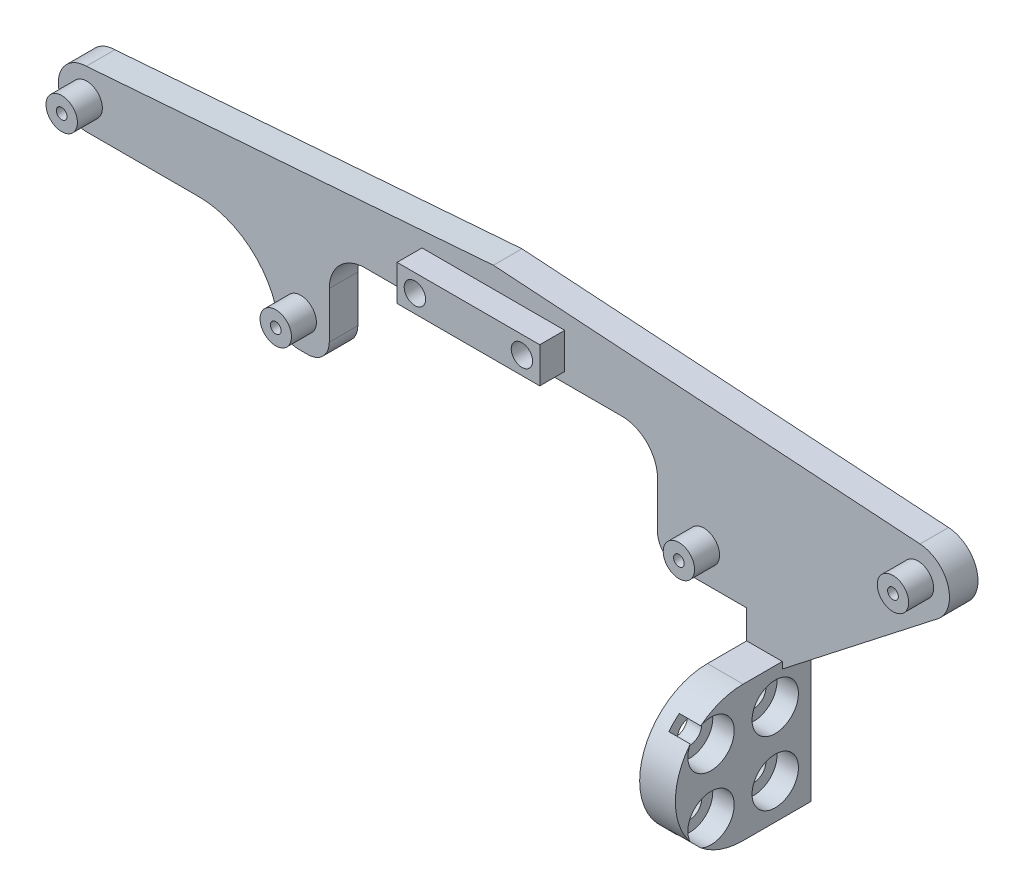
SolidWorks part; units mm, degrees
ref_plane "Front" through (0, 0, 0) normal (0, 0, 1) x (1, 0, 0)
ref_plane "Top" through (0, 0, 0) normal (0, 1, 0) x (1, 0, 0)
ref_plane "Right" through (0, 0, 0) normal (1, 0, 0) x (0, 0, -1)
sketch "Sketch1" plane through (0, 0, 0) normal (0, 0, 1) x (1, 0, 0)
  line L0 (0, 0) -> (59.7902, -3.9348)
  line L1 (62.3996, -11.6782) -> (40.5, -28.7585)
  line L2 (40.5, -28.7585) -> (40.5, -46.844)
  line L3 (40.5, -46.844) -> (35.5, -46.844)
  line L4 (35.5, -46.844) -> (35.5, -23.844)
  line L5 (35.5, -23.844) -> (23, -23.844)
  line L6 (23, -23.844) -> (23, -9.3156)
  line L7 (23, -9.3156) -> (-23, -9.3156)
  line L8 (-23, -9.3156) -> (-23, -23.844)
  line L9 (-23, -23.844) -> (-30, -23.844)
  line L10 (-30, -23.844) -> (-30, -23.6246)
  line L11 (-41.3048, -12.3198) -> (-57, -12.3198)
  line L12 (-57.0499, -4.3684) -> (0, 0)
  arc A0 (59.7902, -3.9348) -> (62.3996, -11.6782) centre (59.5, -8.344) cw
  arc A1 (-30, -23.6246) -> (-41.3048, -12.3198) centre (-41.3048, -23.6246) ccw
  arc A2 (-57, -12.3198) -> (-57.0499, -4.3684) centre (-57, -8.344) cw
  dimension "D7" = 23
  dimension "D8" = 38.5
  dimension "D1" = 46
  dimension "D2" = 5
  dimension "D3" = 19
  dimension "D4" = 12.5
  dimension "D5" = 34
  dimension "D6" = 7
  dimension "D13" = 38.5
extrude "Boss-Extrude1" add sketch "Sketch1" along normal blind 4
sketch "Sketch2" plane through (0, 0, 4) normal (0, 0, 1) x (1, 0, 0)
  circle A0 centre (59.5, -8.344) radius 2.2
  dimension "D1" = 4.4
extrude "Boss-Extrude2" add sketch "Sketch2" along normal blind 3.5
sketch "Sketch3" plane through (0, 0, 7.5) normal (0, 0, 1) x (1, 0, 0)
  circle A0 centre (59.5, -8.344) radius 0.75
  dimension "D1" = 1.5
extrude "Cut-Extrude1" cut sketch "Sketch3" against normal through all
sketch "Sketch4" plane through (0, 0, 4) normal (0, 0, 1) x (1, 0, 0)
  circle A0 centre (29.5, -19.344) radius 2.2
  circle A1 centre (59.5, -8.344) radius 0.75 construction
  dimension "D1" = 4.4
  dimension "D2" = 30
  dimension "D3" = 11
extrude "Boss-Extrude3" add sketch "Sketch4" along normal blind 3.5
sketch "Sketch5" plane through (0, 0, 7.5) normal (0, 0, 1) x (1, 0, 0)
  circle A0 centre (29.5, -19.344) radius 0.75
  dimension "D1" = 1.5
extrude "Cut-Extrude2" cut sketch "Sketch5" against normal through all
sketch "Sketch6" plane through (0, 0, 4) normal (0, 0, 1) x (1, 0, 0)
  circle A0 centre (-57, -8.344) radius 2.2
  dimension "D1" = 4.4
extrude "Boss-Extrude4" add sketch "Sketch6" along normal blind 3.5
sketch "Sketch7" plane through (0, 0, 7.5) normal (0, 0, 1) x (1, 0, 0)
  circle A0 centre (-57, -8.344) radius 0.75
  dimension "D1" = 1.5
extrude "Cut-Extrude3" cut sketch "Sketch7" against normal through all
sketch "Sketch8" plane through (0, 0, 4) normal (0, 0, 1) x (1, 0, 0)
  circle A0 centre (-27, -19.344) radius 2.2
  circle A1 centre (-57, -8.344) radius 0.75 construction
  dimension "D1" = 4.4
  dimension "D2" = 30
  dimension "D3" = 11
extrude "Boss-Extrude5" add sketch "Sketch8" along normal blind 3.5
sketch "Sketch9" plane through (0, 0, 7.5) normal (0, 0, 1) x (1, 0, 0)
  circle A0 centre (-27, -19.344) radius 0.75
  dimension "D1" = 1.5
extrude "Cut-Extrude4" cut sketch "Sketch9" against normal through all
sketch "Sketch10" plane through (0, 0, 4) normal (0, 0, 1) x (1, 0, 0)
  line L1 (-10, -2.8992) -> (10, -2.8992)
  line L2 (-10, -2.8992) -> (-10, -7.8992)
  line L3 (-10, -7.8992) -> (10, -7.8992)
  line L4 (10, -2.8992) -> (10, -7.8992)
  dimension "D1" = 5
  dimension "D2" = 20
  dimension "D3" = 10
extrude "Boss-Extrude6" add sketch "Sketch10" along normal blind 3.5
sketch "Sketch11" plane through (0, 0, 7.5) normal (0, 0, 1) x (1, 0, 0)
  line L0 (10, -2.8992) -> (-10, -2.8992) construction
  line L2 (-10, -2.8992) -> (-10, -7.8992) construction
  circle A0 centre (-7.5, -5.3992) radius 1.5
  circle A1 centre (7.5, -5.3992) radius 1.5
  dimension "D1" = 3
  dimension "D2" = 3
  dimension "D3" = 2.5
  dimension "D4" = 15
  dimension "D5" = 2.5
extrude "Cut-Extrude5" cut sketch "Sketch11" against normal through all
sketch "Sketch12" plane through (40.5, 0, 0) normal (1, 0, 0) x (0, 0, -1)
  line L0 (-4, -46.844) -> (0, -46.844) construction
  line L1 (-4, -46.844) -> (-4, -28.7585) construction
  line L2 (-9.5, -27.844) -> (-4, -27.844)
  line L3 (-4, -28.7585) -> (-4, -11.6782) construction
  line L4 (-4, -27.844) -> (-4, -29.598)
  line L5 (-9.5, -46.844) -> (-4, -46.844)
  line L6 (-4, -46.844) -> (-4, -45.0899)
  line L7 (-4, -29.598) -> (-4, -45.0899)
  line L9 (-9.5, -27.844) -> (-4, -27.844)
  line L10 (-9.5, -27.844) -> (-9.5, -46.844)
  line L11 (-9.5, -46.844) -> (-4, -46.844)
  line L12 (-4, -27.844) -> (-4, -46.844)
  circle A0 centre (-9.5, -37.344) radius 9.5
  line M4 (-4, -28.7585) -> (-4, -46.844)
  dimension "D1" = 19
  dimension "D2" = 9.5
  dimension "D3" = 5.5
extrude "Boss-Extrude8" add sketch "Sketch12" against normal blind 5 contours A0 L4 L2 M4 | A0 L5 M4
hole_wizard "CBORE for M3 SHCS1" positions "3DSketch1" profile "Sketch14" counterbore size "M3" standard "ANSI Metric" end condition through all
sketch3d "3DSketch1"
  line L0 (40.5, -27.844, 9.5) -> (40.5, -27.844, 4) construction
  line L1 (40.5, -46.844, 0) -> (40.5, -28.7585, 0) construction
  point P0 (40.5, -32.844, 14)
  point P2 (40.5, -32.844, 5)
  point P4 (40.5, -41.844, 14)
  point P6 (40.5, -41.844, 5)
  point P20 (40.5, -41.844, 5)
  dimension "D1" = 5
  dimension "D4" = 5
  dimension "D2" = 9
  dimension "D3" = 9
sketch "Sketch14" plane through (40.5, -32.844, 14) normal (0, 1, 0) x (0, 0, -1)
  line L0 (0, 0) -> (0, 101.4759)
  line L1 (0, 101.4759) -> (1.7, 101.4759)
  line L3 (1.7, 101.4759) -> (1.7, 3)
  line L4 (1.7, 3) -> (3.25, 3)
  line L5 (3.25, 3) -> (3.25, 0)
  line L7 (3.25, 0) -> (0, 0)
  line L11 (0, -6.35) -> (0, 107.95) construction
  dimension "Thru Hole Dia." = 3.4
  dimension "Thru Hole Depth" = 101.4759
  dimension "C'Bore Dia." = 6.5
  dimension "C'Bore Depth" = 3
fillet "Fillet1" radius 5 2 edges at (-23, -9.3156, 2) (23, -9.3156, 2)
fillet "Fillet2" radius 3 3 edges at (-30, -23.844, 2) (23, -23.844, 2) (-23, -23.844, 2)
